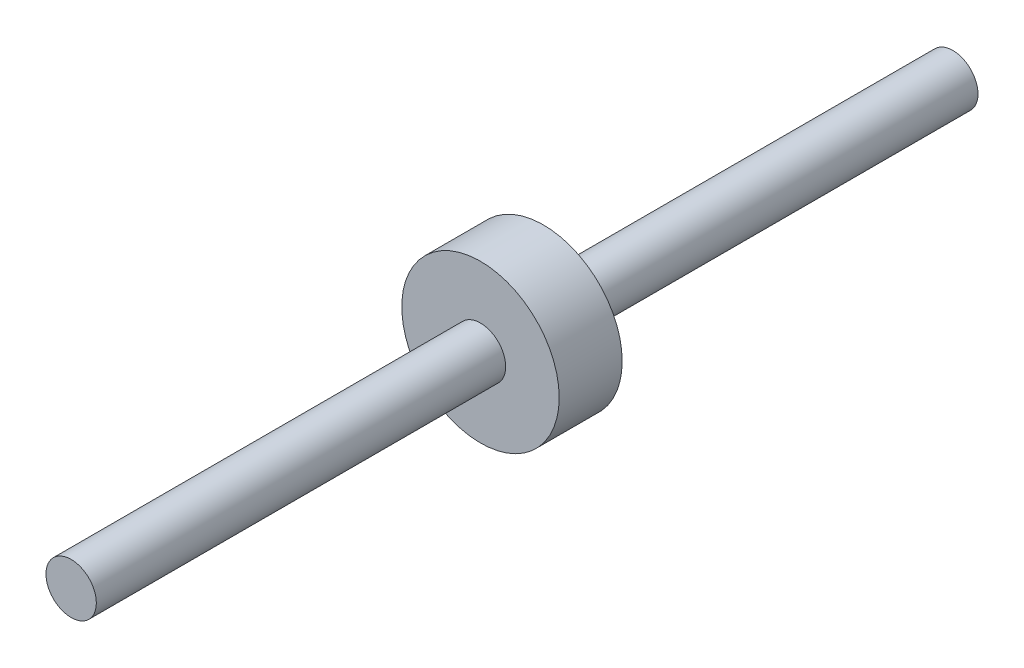
SolidWorks part; units mm, degrees
material "Stal stopowa"
ref_plane "Płaszczyzna przednia" through (0, 0, 0) normal (0, 0, 1) x (1, 0, 0)
ref_plane "Płaszczyzna górna" through (0, 0, 0) normal (0, 1, 0) x (1, 0, 0)
ref_plane "Płaszczyzna prawa" through (0, 0, 0) normal (1, 0, 0) x (0, 0, -1)
sketch "Szkic1" plane through (0, 0, 0) normal (0, 1, 0) x (1, 0, 0)
  line L0 (-4, 75) -> (-4, 140)
  line L1 (0, 0) -> (-4, 0)
  line L2 (0, 0) -> (0, 140)
  line L3 (0, 140) -> (-4, 140)
  line L4 (-4, 0) -> (-4, 65)
  line L8 (0, 75) -> (0, 65)
  line L9 (-12.5, 75) -> (-4, 75)
  line L10 (-12.5, 75) -> (-12.5, 65)
  line L11 (-12.5, 65) -> (-4, 65)
  dimension "D1" = 140
  dimension "D2" = 65
  dimension "D3" = 12.5
  dimension "D5" = 4
revolve "Obrót1" add sketch "Szkic1" angle 360 about L2
